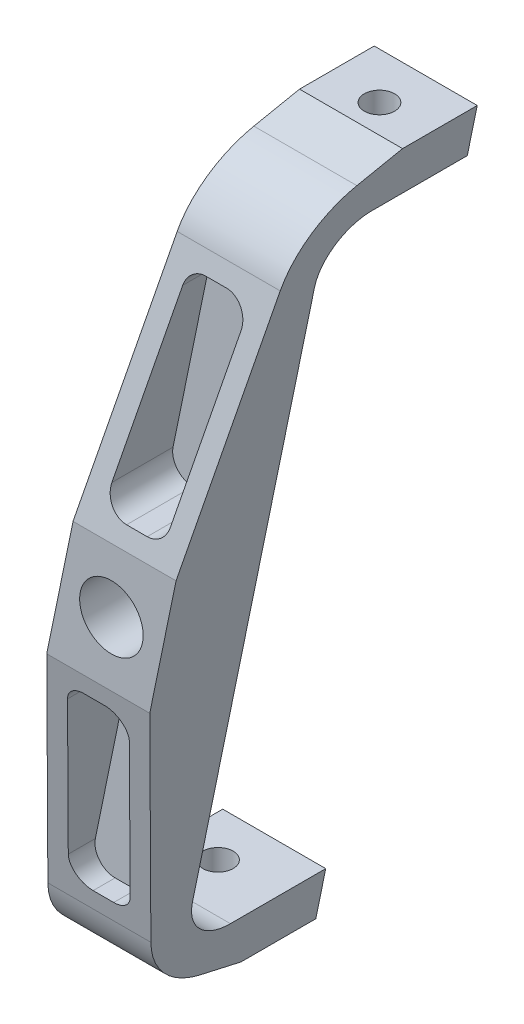
SolidWorks part; units mm, degrees
other "Markup1"
sketch "Sketch6" plane through (39.3536, 123.4271, -45) normal (0.998, 0.0328, -0.0532) x (-0.0595, 0.2351, -0.9701)
other "Markup2"
sketch "Sketch7" plane through (39.3536, 123.4271, -45) normal (0.9999, 0.0057, -0.0131) x (0.0031, -0.9818, -0.1901)
other "Markup4"
sketch "Sketch9" plane through (-39.3536, 123.4271, 27) normal (-0.9915, 0.1233, 0.0413) x (-0.1205, -0.9906, 0.0646)
other "Markup5"
sketch "Sketch12" plane through (-39.3536, 123.4271, 28.5) normal (-0.7749, 0.0474, 0.6304) x (0.632, 0.0395, 0.7739)
material "6061-T6 (SS)"
ref_plane "Front Plane" through (0, 0, 0) normal (0, 0, 1) x (1, 0, 0)
ref_plane "Top Plane" through (0, 0, 0) normal (0, 1, 0) x (1, 0, 0)
ref_plane "Right Plane" through (0, 0, 0) normal (1, 0, 0) x (0, 0, -1)
sketch "Sketch1" plane through (0, 0, 0) normal (0, 0, 1) x (1, 0, 0)
  line L0 (0, 203) -> (0, -203) construction
  line L1 (0, -266) -> (0, -203) construction
  line L2 (0, -266) -> (-54.7044, -266) construction
  line L3 (54.7044, 266) -> (-54.7044, -266) construction
  line L8 (-26.0577, -126.7054) -> (26.0577, 126.7054) construction
  line L9 (-9.1928, -123.5075) -> (41.6072, 123.5075)
  line L14 (-41.6072, -123.5075) -> (9.1928, 123.5075)
  line L15 (41.6072, 123.5075) -> (9.1928, 123.5075)
  line L16 (-41.6072, -123.5075) -> (-9.1928, -123.5075)
  line L17 (-41.6072, -123.5075) -> (10.5081, 129.9032) construction
  line L18 (25.4, 123.5075) -> (25.4, 134.62) construction
  line L19 (-10.5081, -129.9032) -> (41.6072, 123.5075) construction
  line L20 (-25.4, -123.5075) -> (-25.4, -134.62) construction
  circle A1 centre (0, 0) radius 10
  circle A2 centre (0, 0) radius 170.5 construction
  point P1 (-25.4, -123.5075)
  point P6 (0, 0)
  point P10 (0, -170.5)
  point P12 (0, 0)
  point P16 (0, -189.8)
  point P17 (0, 0)
  point P21 (25.4, 123.5075)
  dimension "D4" = 341
  dimension "D9" = 20
  dimension "D1" = 203
  dimension "D2" = 63
  dimension "D3" = 50.8
  dimension "D5" = 95.5
  dimension "D6" = 76.2
  dimension "D7" = 15.875
  dimension "D8" = 15.875
  dimension "D10" = 247.015
  dimension "D11" = 11.1125
  dimension "D12" = 269.24
extrude "Boss-Extrude1" add sketch "Sketch1" along normal blind 28.5
sketch "Sketch2" plane through (0, 0, 0) normal (0, 0, -1) x (-1, 0, 0)
  line L0 (-38.473, 108.2675) -> (-6.0586, 108.2675)
  line L1 (6.0586, -108.2675) -> (38.473, -108.2675)
  line L4 (-9.1928, 123.5075) -> (-41.6072, 123.5075)
  line L5 (-41.6072, 123.5075) -> (9.1928, -123.5075)
  line L6 (9.1928, -123.5075) -> (41.6072, -123.5075)
  line L7 (41.6072, -123.5075) -> (-9.1928, 123.5075)
  line L8 (-9.1928, 123.5075) -> (-41.6072, 123.5075)
  line L9 (-41.6072, 123.5075) -> (9.1928, -123.5075)
  line L10 (9.1928, -123.5075) -> (41.6072, -123.5075)
  line L11 (41.6072, -123.5075) -> (-9.1928, 123.5075)
  line M7 (-9.1928, 123.5075) -> (-41.6072, 123.5075)
  line M8 (-41.6072, 123.5075) -> (9.1928, -123.5075)
  line M9 (9.1928, -123.5075) -> (41.6072, -123.5075)
  line M10 (41.6072, -123.5075) -> (-9.1928, 123.5075)
  dimension "D2" = 15.24
  dimension "D3" = 15.24
  dimension "D1" = 0
extrude "Boss-Extrude2" add sketch "Sketch2" along normal blind 45 contours L0 M8 M10 M7 | L1 M8 M9 M10
sketch "Sketch4" plane through (0, 123.5075, 0) normal (0, 1, 0) x (1, 0, 0)
  line L0 (25.4, -28.5) -> (25.4, 45) construction
  line L1 (0, 30.433) -> (85.2766, 30.433) construction
  line L2 (0, 30.433) -> (85.2766, 30.433)
  line L4 (41.6072, -28.5) -> (41.6072, 45)
  line L5 (41.6072, 45) -> (9.1928, 45)
  line L6 (9.1928, 45) -> (9.1928, -28.5)
  line L7 (9.1928, -28.5) -> (41.6072, -28.5)
  line L8 (41.6072, -28.5) -> (41.6072, 45)
  line L9 (41.6072, 45) -> (9.1928, 45)
  line L10 (9.1928, 45) -> (9.1928, -28.5)
  line L11 (9.1928, -28.5) -> (41.6072, -28.5)
  circle A0 centre (25.4, 30.433) radius 4.7625
  point P6 (25.4, 30.433)
  dimension "D1" = 0
extrude "Cut-Extrude1" cut sketch "Sketch4" against normal blind 30 contours L0 L2 A0 | L2 L0 A0 | A0 L0 L2 | L0 A0 L2
pattern_circular "CirPattern1" count 2 over 360 about axis through (0, 0, -30.433) along (0, 1, 0) of "Cut-Extrude1"
chamfer "Chamfer1" distance 50 angle 15 2 edges at (-25.4, -123.5075, 28.5) (25.4, 123.5075, 28.5)
fillet "Fillet3" radius 15 2 edges at (22.2658, 108.2675, 0) (-22.2658, -108.2675, 0)
chamfer "Chamfer2" distance 90 angle 8 2 edges at (-22.6447, -110.11, 28.5) (22.6447, 110.11, 28.5)
sketch "Sketch10" plane through (0, 0, 0) normal (1, 0, 0) x (0, 0, -1)
  line L0 (-28.5, 20.11) -> (-11.939, 98.9279)
  line L1 (-28.5, 20.11) -> (-33.9568, 23.5224)
  line L2 (-33.9568, 23.5224) -> (-24.6981, 128.3877)
  line L3 (-24.6981, 128.3877) -> (7.8754, 119.8568)
  line L5 (21.5, 123.5075) -> (-15.3564, 113.6319) construction
  line L6 (21.5, 123.5075) -> (-15.3564, 113.6319) construction
  arc A0 (15, 108.2675) -> (0, 93.2675) centre (15, 93.2675) ccw construction
  arc A1 (15, 108.2675) -> (0, 93.2675) centre (15, 93.2675) ccw construction
  arc A2 (7.8754, 119.8568) -> (-11.939, 98.9279) centre (15, 93.2675) ccw
  point P14 (7.8754, 119.8568)
extrude "Cut-Extrude2" cut sketch "Sketch10" against normal through all both and the other way through all
mirror "Mirror1" about plane through (0, 0, 0) normal (0, 1, 0) of "Cut-Extrude2"
sketch "Sketch11" plane through (0, 0, 28.5) normal (0, 0, 1) x (1, 0, 0)
  line L0 (4.1378, 98.9279) -> (36.5523, 98.9279) construction
  line L1 (4.1378, 98.9279) -> (36.5523, 98.9279) construction
  line L2 (36.5523, 98.9279) -> (20.343, 20.11) construction
  line L3 (36.5523, 98.9279) -> (20.343, 20.11) construction
  line L4 (-12.0715, 20.11) -> (-20.343, -20.11)
  line L5 (-20.343, -20.11) -> (12.0715, -20.11)
  line L6 (12.0715, -20.11) -> (20.343, 20.11)
  line L7 (20.343, 20.11) -> (-12.0715, 20.11)
  line L8 (-12.0715, 20.11) -> (-20.343, -20.11)
  line L10 (12.0715, -20.11) -> (20.343, 20.11)
  line L11 (20.343, 20.11) -> (-12.0715, 20.11) construction
  line L12 (-12.0715, 20.11) -> (4.1378, 98.9279) construction
  line L13 (-12.0715, 20.11) -> (4.1378, 98.9279) construction
  line L14 (-3.9668, 59.5189) -> (28.4476, 59.5189) construction
  line L15 (20.3451, 98.9279) -> (4.1357, 20.11) construction
  line L16 (-5.8517, 18.8309) -> (-5.5886, 20.11)
  line L17 (9.3148, 92.5779) -> (28.7635, 92.5779)
  line L18 (28.7635, 92.5779) -> (15.1292, 26.2812)
  line L23 (-4.3168, 26.294) -> (9.3148, 92.5779)
  line L24 (-36.5523, -98.9279) -> (-4.1378, -98.9279) construction
  line L25 (15.1292, 26.2812) -> (-4.3168, 26.294)
  line L26 (-5.8517, 18.8309) -> (9.3148, 92.5779) construction
  line L27 (28.7635, 92.5779) -> (14.1231, 21.3892) construction
  line L28 (-4.1378, -98.9279) -> (12.0715, -20.11) construction
  line L29 (-20.343, -20.11) -> (-36.5523, -98.9279) construction
  line L30 (-20.343, -20.11) -> (12.0715, -20.11) construction
  line L31 (-36.5523, -98.9279) -> (-4.1378, -98.9279)
  line L32 (-4.1378, -98.9279) -> (12.0715, -20.11)
  line L33 (-20.343, -20.11) -> (-36.5523, -98.9279)
  line L34 (-20.343, -20.11) -> (12.0715, -20.11)
  line L35 (-15.166, -26.46) -> (4.2827, -26.46)
  line L36 (-9.3148, -92.5779) -> (4.2827, -26.46)
  line L37 (-28.7635, -92.5779) -> (-9.3148, -92.5779)
  line L38 (-15.166, -26.46) -> (-28.7635, -92.5779)
  point P18 (27.5728, 26.3797)
  point P19 (-17.6556, 26.3797)
  dimension "D2" = 6.35
  dimension "D1" = 0
  dimension "D3" = 6.35
extrude "Cut-Extrude4" cut sketch "Sketch11" against normal offset from surface (22.15 mm away) 6.35 contours L25 L18 L17 L23 | L35 L38 L37 L36 up to face at (0, 0, 0)
fillet "Fillet6" radius 6.35 8 edges at (15.1292, 26.2812, 16.7767) (-4.3168, 26.294, 16.7753) (28.7635, 92.5779, 9.8116) (9.3148, 92.5779, 9.8116) (-9.3148, -92.5779, 9.8116) (-28.7635, -92.5779, 9.8116) (4.2827, -26.46, 16.7579) (-15.166, -26.46, 16.7579)
move or copy body "Body-Move/Copy2" [suppressed] bodies to move or copy 109
move or copy body "Body-Move/Copy1" [suppressed] bodies to move or copy 109
